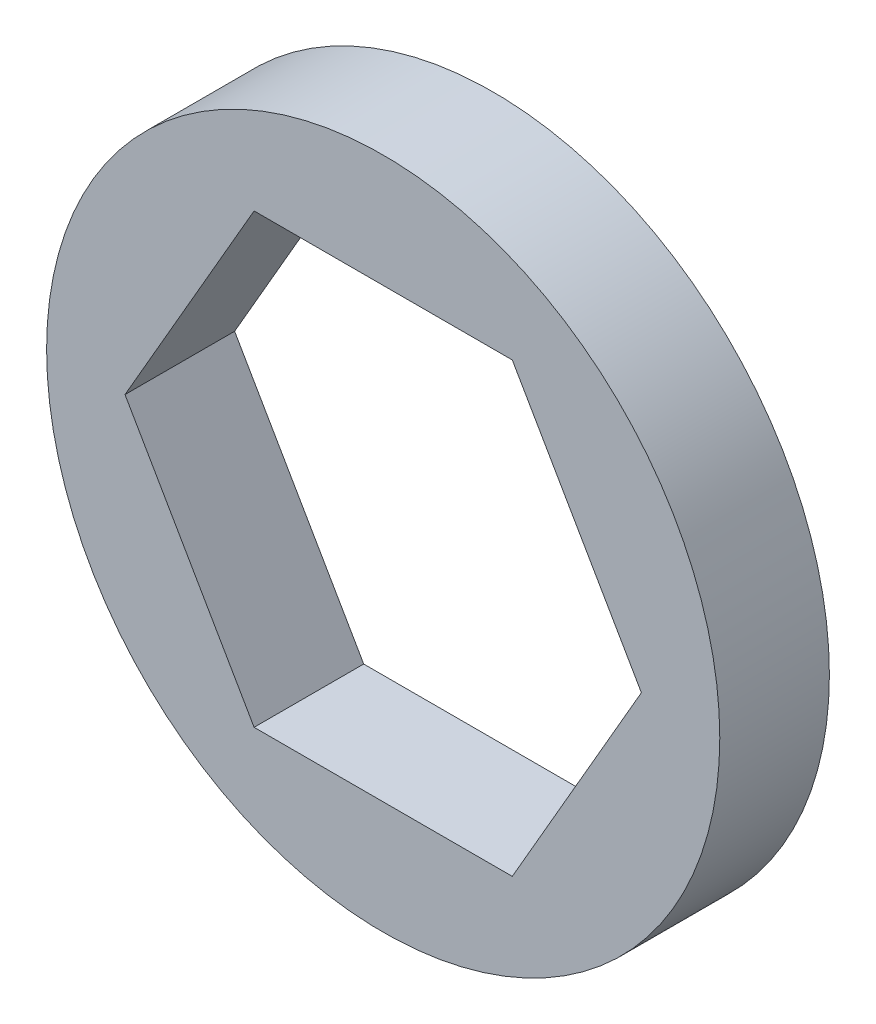
SolidWorks part; units mm, degrees
material "ABS PC"
ref_plane "Front Plane" through (0, 0, 0) normal (0, 0, 1) x (1, 0, 0)
ref_plane "Top Plane" through (0, 0, 0) normal (0, 1, 0) x (1, 0, 0)
ref_plane "Right Plane" through (0, 0, 0) normal (1, 0, 0) x (0, 0, -1)
ref_plane "Plane4" through (0, 0, 3.175) normal (0, 0, 1) x (1, 0, 0)
sketch "Sketch1" plane through (0, 0, 3.175) normal (0, 0, 1) x (1, 0, 0)
  line L0 (-3.7395, 6.477) -> (3.7395, 6.477)
  line L1 (3.7395, 6.477) -> (7.479, 0)
  line L2 (7.479, 0) -> (3.7395, -6.477)
  line L3 (3.7395, -6.477) -> (-3.7395, -6.477)
  line L4 (-3.7395, -6.477) -> (-7.479, 0)
  line L5 (-7.479, 0) -> (-3.7395, 6.477)
  circle A0 centre (0, 0) radius 9.75
extrude "Boss-Extrude1" add sketch "Sketch1" against normal blind 3.175
ref_plane "Plane5" through (0, 0, -3.175) normal (0, 0, 1) x (1, 0, 0)
